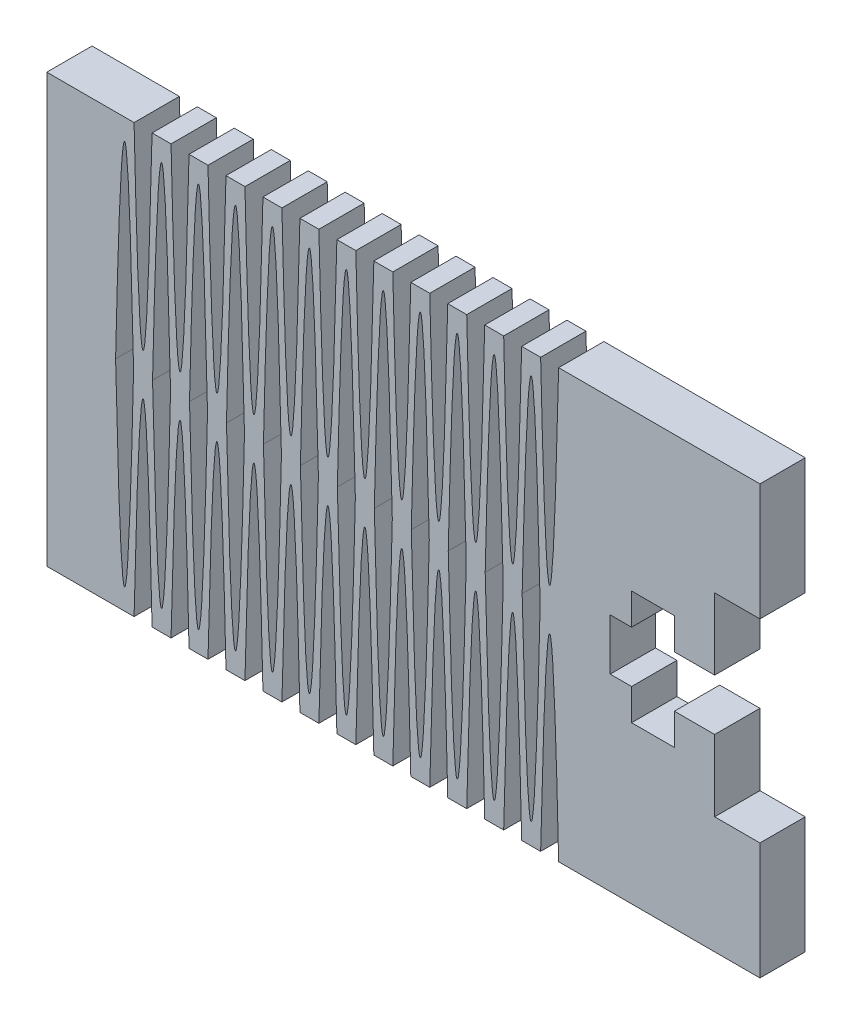
SolidWorks part; units mm, degrees
ref_plane "정면" through (0, 0, 0) normal (0, 0, 1) x (1, 0, 0)
ref_plane "윗면" through (0, 0, 0) normal (0, 1, 0) x (1, 0, 0)
ref_plane "우측면" through (0, 0, 0) normal (1, 0, 0) x (0, 0, -1)
sketch "Sketch1" plane through (0, 0, 0) normal (0, 0, 1) x (1, 0, 0)
  line L52 (-46.9113, 77.2573) -> (-46.9113, 85.4573)
  line L53 (-96.9113, 55.4573) -> (-90.7903, 55.4572)
  line L54 (-96.9113, 55.4573) -> (-96.9113, 85.4573)
  line L55 (-89.5287, 55.4573) -> (-88.1991, 55.4573)
  line L56 (-46.9113, 55.4573) -> (-46.9113, 63.6573)
  line L57 (-46.9113, 77.2573) -> (-50.0863, 77.2573)
  line L58 (-50.0863, 77.2573) -> (-50.0863, 72.2573)
  line L59 (-50.0863, 72.2573) -> (-52.9113, 72.2573)
  line L60 (-52.9113, 72.2573) -> (-52.9113, 74.4573)
  line L61 (-52.9113, 74.4573) -> (-55.9113, 74.4573)
  line L62 (-55.9113, 74.4573) -> (-55.9113, 72.2573)
  line L63 (-55.9113, 72.2573) -> (-57.4113, 72.2573)
  line L64 (-57.4113, 68.6573) -> (-57.4113, 72.2573)
  line L65 (-55.9113, 68.6573) -> (-57.4113, 68.6573)
  line L66 (-55.9113, 66.4573) -> (-55.9113, 68.6573)
  line L67 (-52.9113, 66.4573) -> (-55.9113, 66.4573)
  line L68 (-52.9113, 68.6573) -> (-52.9113, 66.4573)
  line L69 (-50.0863, 68.6573) -> (-52.9113, 68.6573)
  line L70 (-50.0863, 63.6573) -> (-50.0863, 68.6573)
  line L71 (-46.9113, 63.6573) -> (-50.0863, 63.6573)
  line L72 (-61.0251, 85.4573) -> (-46.9113, 85.4573)
  line L73 (-63.6163, 85.4573) -> (-62.2867, 85.4573)
  line L74 (-66.2075, 85.4573) -> (-64.8779, 85.4573)
  line L75 (-76.5724, 85.4573) -> (-75.2428, 85.4573)
  line L76 (-79.1636, 85.4573) -> (-77.8341, 85.4573)
  line L77 (-81.7552, 85.4573) -> (-80.4252, 85.4573)
  line L78 (-84.3464, 85.4573) -> (-83.0169, 85.4573)
  line L79 (-86.9376, 85.4573) -> (-85.608, 85.4573)
  line L80 (-86.9375, 55.4573) -> (-85.608, 55.4573)
  line L81 (-84.3464, 55.4573) -> (-83.0169, 55.4573)
  line L82 (-81.7552, 55.4573) -> (-80.4252, 55.4573)
  line L83 (-79.1636, 55.4573) -> (-77.8341, 55.4573)
  line L84 (-76.5724, 55.4573) -> (-75.243, 55.4573)
  line L85 (-73.9813, 55.4573) -> (-72.6518, 55.4573)
  line L86 (-68.7985, 55.4573) -> (-67.469, 55.4573)
  line L87 (-66.2074, 55.4573) -> (-64.8779, 55.4573)
  line L88 (-63.6163, 55.4573) -> (-62.2867, 55.4573)
  line L89 (-61.0251, 55.4573) -> (-46.9113, 55.4573)
  line L90 (-71.3902, 55.4572) -> (-70.0602, 55.4572)
  line L91 (-90.7904, 85.4572) -> (-96.9113, 85.4573)
  line L92 (-89.5288, 85.4573) -> (-88.1993, 85.4573)
  line L93 (-73.9812, 85.4573) -> (-72.6517, 85.4573)
  line L94 (-71.39, 85.4572) -> (-70.0603, 85.4572)
  line L95 (-68.7987, 85.4575) -> (-67.4691, 85.4575)
  line L96 (-63.5823, 70.4599) -> (-63.5823, 70.4546)
  line L97 (-64.9119, 70.4599) -> (-64.9119, 70.4546)
  line L99 (-68.7647, 70.4546) -> (-68.7647, 70.4599)
  line L100 (-70.0942, 70.4546) -> (-70.0942, 70.4599)
  line L101 (-73.9476, 70.4546) -> (-73.9476, 70.4599)
  line L102 (-75.2772, 70.4546) -> (-75.2772, 70.4599)
  line L103 (-79.13, 70.4547) -> (-79.13, 70.46)
  line L104 (-80.4595, 70.4547) -> (-80.4595, 70.46)
  line L105 (-84.3126, 70.4547) -> (-84.3126, 70.46)
  line L106 (-85.6421, 70.4547) -> (-85.6421, 70.46)
  line L107 (-89.4949, 70.4546) -> (-89.4949, 70.4599)
  line L108 (-90.8245, 70.4546) -> (-90.8245, 70.4599)
  spline S2 degree 2 poles (-61.0251, 85.4573) (-61.6559, 58.4024) (-62.2867, 85.4573) knots 0 0 0 1 1 1
  spline S3 degree 2 poles (-61.0251, 55.4573) (-61.6559, 82.5122) (-62.2867, 55.4573) knots 0 0 0 1 1 1
  spline S4 degree 2 poles (-62.3207, 70.4573) (-62.9514, 97.5161) (-63.5823, 70.4599) knots 0 0 0 1 1 1
  spline S5 degree 2 poles (-62.3207, 70.4573) (-62.9514, 43.3984) (-63.5823, 70.4546) knots 0 0 0 1 1 1
  spline S6 degree 2 poles (-64.8779, 55.4573) (-64.2471, 82.5122) (-63.6163, 55.4573) knots 0 0 0 1 1 1
  spline S7 degree 2 poles (-64.8779, 85.4573) (-64.2471, 58.4024) (-63.6163, 85.4573) knots 0 0 0 1 1 1
  spline S8 degree 2 poles (-66.1735, 70.4573) (-65.5428, 43.3984) (-64.9119, 70.4546) knots 0 0 0 1 1 1
  spline S9 degree 2 poles (-66.1735, 70.4573) (-65.5428, 97.5161) (-64.9119, 70.4599) knots 0 0 0 1 1 1
  spline S10 degree 2 poles (-66.2074, 55.4573) (-66.8383, 82.5122) (-67.469, 55.4573) knots 0 0 0 1 1 1
  spline S11 degree 2 poles (-70.0602, 55.4572) (-69.4295, 82.5122) (-68.7985, 55.4573) knots 0 0 0 1 1 1
  spline S12 degree 2 poles (-70.0603, 85.4572) (-69.4294, 58.4022) (-68.7987, 85.4575) knots 0 0 0 1 1 1
  spline S13 degree 2 poles (-66.2075, 85.4573) (-66.8382, 58.4022) (-67.4691, 85.4575) knots 0 0 0 1 1 1
  spline S14 degree 2 poles (-67.503, 70.4573) (-68.1335, 43.3984) (-68.7647, 70.4546) knots 0 0 0 1 1 1
  spline S15 degree 2 poles (-71.3558, 70.4572) (-70.7249, 43.3984) (-70.0942, 70.4546) knots 0 0 0 1 1 1
  spline S16 degree 2 poles (-71.3558, 70.4572) (-70.7254, 97.5161) (-70.0942, 70.4599) knots 0 0 0 1 1 1
  spline S17 degree 2 poles (-67.503, 70.4573) (-68.134, 97.5161) (-68.7647, 70.4599) knots 0 0 0 1 1 1
  spline S18 degree 2 poles (-71.3902, 55.4572) (-72.0209, 82.5122) (-72.6518, 55.4573) knots 0 0 0 1 1 1
  spline S19 degree 2 poles (-75.243, 55.4573) (-74.612, 82.5122) (-73.9813, 55.4573) knots 0 0 0 1 1 1
  spline S20 degree 2 poles (-76.5724, 55.4573) (-77.2033, 82.5122) (-77.8341, 55.4573) knots 0 0 0 1 1 1
  spline S21 degree 2 poles (-80.4252, 55.4573) (-79.7944, 82.5122) (-79.1636, 55.4573) knots 0 0 0 1 1 1
  spline S22 degree 2 poles (-80.4252, 85.4573) (-79.7944, 58.4024) (-79.1636, 85.4573) knots 0 0 0 1 1 1
  spline S23 degree 2 poles (-76.5724, 85.4573) (-77.2033, 58.4024) (-77.8341, 85.4573) knots 0 0 0 1 1 1
  spline S24 degree 2 poles (-75.2428, 85.4573) (-74.6121, 58.4023) (-73.9812, 85.4573) knots 0 0 0 1 1 1
  spline S25 degree 2 poles (-71.39, 85.4572) (-72.021, 58.4023) (-72.6517, 85.4573) knots 0 0 0 1 1 1
  spline S26 degree 2 poles (-72.686, 70.4572) (-73.3172, 43.3984) (-73.9476, 70.4546) knots 0 0 0 1 1 1
  spline S27 degree 2 poles (-76.5388, 70.4573) (-75.9086, 43.3984) (-75.2772, 70.4546) knots 0 0 0 1 1 1
  spline S28 degree 2 poles (-77.8683, 70.4573) (-78.4993, 43.3985) (-79.13, 70.4547) knots 0 0 0 1 1 1
  spline S29 degree 2 poles (-81.7211, 70.4574) (-81.0907, 43.3985) (-80.4595, 70.4547) knots 0 0 0 1 1 1
  spline S30 degree 2 poles (-81.7211, 70.4574) (-81.0902, 97.5162) (-80.4595, 70.46) knots 0 0 0 1 1 1
  spline S31 degree 2 poles (-77.8683, 70.4573) (-78.4988, 97.5162) (-79.13, 70.46) knots 0 0 0 1 1 1
  spline S32 degree 2 poles (-76.5388, 70.4573) (-75.9076, 97.5161) (-75.2772, 70.4599) knots 0 0 0 1 1 1
  spline S33 degree 2 poles (-72.686, 70.4572) (-73.3162, 97.5161) (-73.9476, 70.4599) knots 0 0 0 1 1 1
  spline S34 degree 2 poles (-81.7552, 55.4573) (-82.386, 82.5122) (-83.0169, 55.4573) knots 0 0 0 1 1 1
  spline S35 degree 2 poles (-85.608, 55.4573) (-84.9772, 82.5122) (-84.3464, 55.4573) knots 0 0 0 1 1 1
  spline S36 degree 2 poles (-86.9375, 55.4573) (-87.5684, 82.5122) (-88.1991, 55.4573) knots 0 0 0 1 1 1
  spline S37 degree 2 poles (-90.7903, 55.4572) (-90.1596, 82.5122) (-89.5287, 55.4573) knots 0 0 0 1 1 1
  spline S38 degree 2 poles (-90.7904, 85.4572) (-90.1595, 58.4023) (-89.5288, 85.4573) knots 0 0 0 1 1 1
  spline S39 degree 2 poles (-86.9376, 85.4573) (-87.5683, 58.4023) (-88.1993, 85.4573) knots 0 0 0 1 1 1
  spline S40 degree 2 poles (-85.608, 85.4573) (-84.9772, 58.4024) (-84.3464, 85.4573) knots 0 0 0 1 1 1
  spline S41 degree 2 poles (-81.7552, 85.4573) (-82.386, 58.4024) (-83.0169, 85.4573) knots 0 0 0 1 1 1
  spline S42 degree 2 poles (-83.0509, 70.4574) (-83.6814, 43.3985) (-84.3126, 70.4547) knots 0 0 0 1 1 1
  spline S43 degree 2 poles (-86.9037, 70.4573) (-86.2728, 43.3985) (-85.6421, 70.4547) knots 0 0 0 1 1 1
  spline S44 degree 2 poles (-88.2333, 70.4573) (-88.8635, 43.3984) (-89.4949, 70.4546) knots 0 0 0 1 1 1
  spline S45 degree 2 poles (-92.0861, 70.4572) (-91.4549, 43.3984) (-90.8245, 70.4546) knots 0 0 0 1 1 1
  spline S46 degree 2 poles (-92.0861, 70.4572) (-91.4559, 97.5161) (-90.8245, 70.4599) knots 0 0 0 1 1 1
  spline S47 degree 2 poles (-88.2333, 70.4573) (-88.8645, 97.5161) (-89.4949, 70.4599) knots 0 0 0 1 1 1
  spline S48 degree 2 poles (-86.9037, 70.4573) (-86.2733, 97.5162) (-85.6421, 70.46) knots 0 0 0 1 1 1
  spline S49 degree 2 poles (-83.0509, 70.4574) (-83.6819, 97.5162) (-84.3126, 70.46) knots 0 0 0 1 1 1
extrude "Boss-Extrude1" add sketch "Sketch1" along normal blind 3.175
